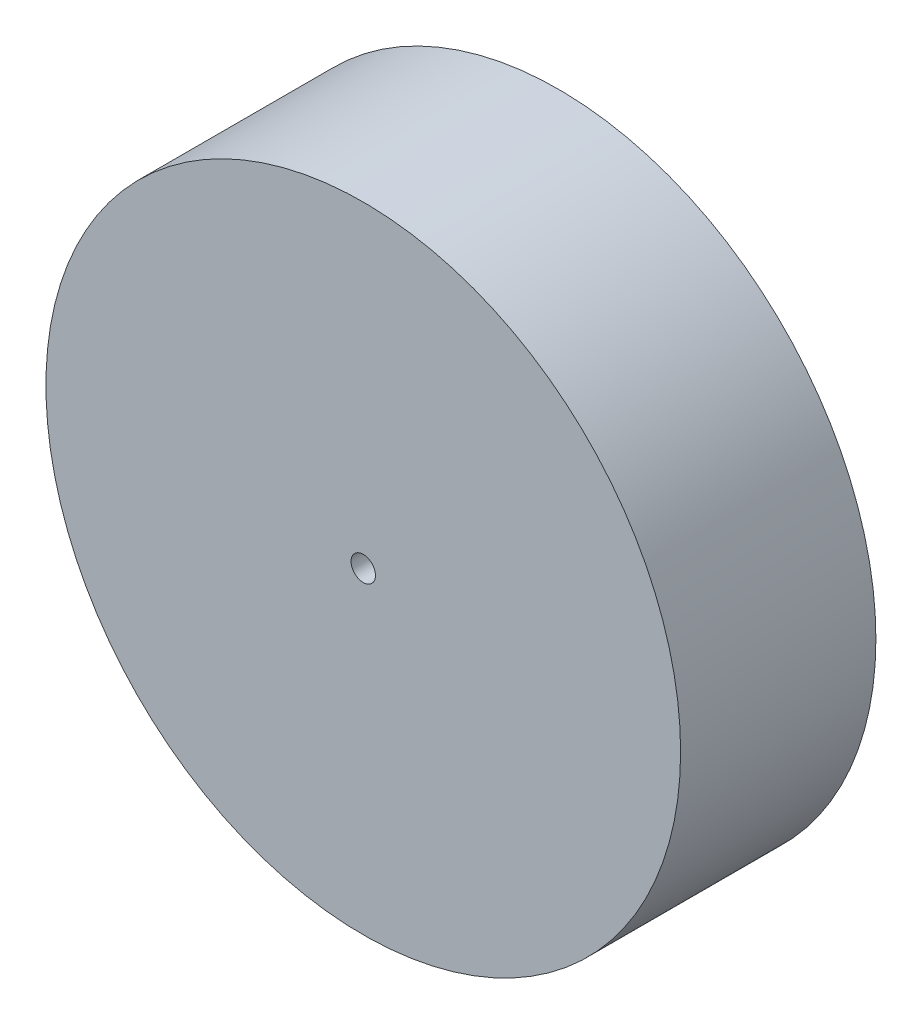
SolidWorks part; units mm, degrees
ref_plane "Front Plane" through (0, 0, 0) normal (0, 0, 1) x (1, 0, 0)
ref_plane "Top Plane" through (0, 0, 0) normal (0, 1, 0) x (1, 0, 0)
ref_plane "Right Plane" through (0, 0, 0) normal (1, 0, 0) x (0, 0, -1)
sketch "Sketch1" plane through (0, 0, 0) normal (0, 0, 1) x (1, 0, 0)
  circle A0 centre (0, 0) radius 65
  dimension "D1" = 130
extrude "Boss-Extrude1" add sketch "Sketch1" along normal blind 40
sketch "Sketch2" plane through (0, 0, 0) normal (0, 0, 1) x (1, 0, 0)
  circle A0 centre (0, 0) radius 2.5
  dimension "D1" = 5
extrude "Cut-Extrude1" cut sketch "Sketch2" along normal through all
